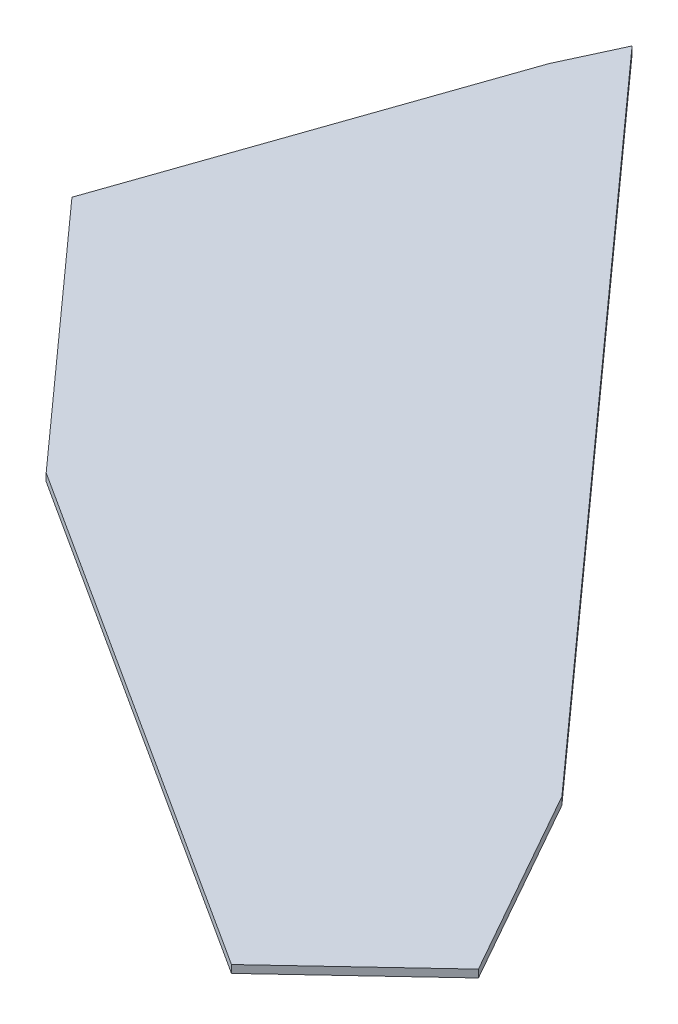
SolidWorks part; units mm, degrees
ref_plane "Plan de face" through (0, 0, 0) normal (0, 0, 1) x (1, 0, 0)
ref_plane "Plan de dessus" through (0, 0, 0) normal (0, 1, 0) x (1, 0, 0)
ref_plane "Plan de droite" through (0, 0, 0) normal (1, 0, 0) x (0, 0, -1)
sketch "Esquisse1" plane through (0, 0, 0) normal (0, 1, 0) x (1, 0, 0)
  line L0 (-26.8481, 157.7915) -> (-58.8222, 65.5371)
  line L1 (-58.8222, 65.5371) -> (0, 0)
  line L2 (0, 0) -> (135.0771, -86.7989)
  line L3 (135.0771, -86.7989) -> (168.2844, -55.6744)
  line L4 (168.2844, -55.6744) -> (140.2245, -5.8724)
  line L5 (140.2245, -5.8724) -> (-19.4444, 172.0235)
  line L6 (-19.4444, 172.0235) -> (-20.0213, 172.5796)
  line L7 (-20.0213, 172.5796) -> (-26.8481, 157.7915)
  point P8 (0, 0)
extrude "Boss.-Extru.1" add sketch "Esquisse1" along normal blind 2
